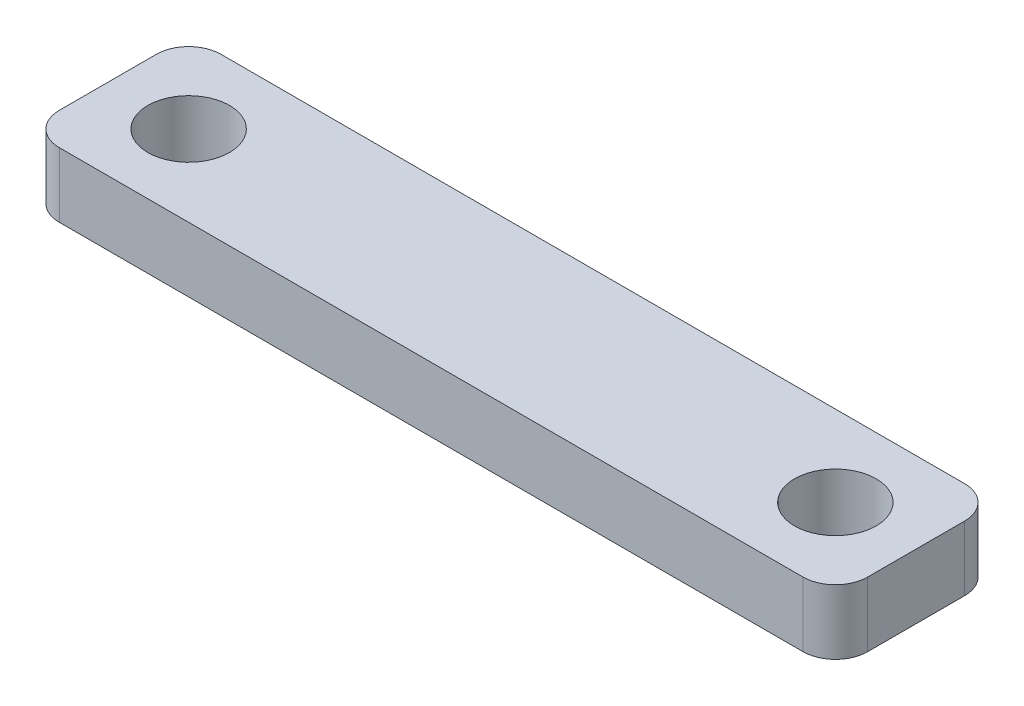
SolidWorks part; units mm, degrees
material "Thornel Mat VMA"
ref_plane "前视基准面" through (0, 0, 0) normal (0, 0, 1) x (1, 0, 0)
ref_plane "上视基准面" through (0, 0, 0) normal (0, 1, 0) x (1, 0, 0)
ref_plane "右视基准面" through (0, 0, 0) normal (1, 0, 0) x (0, 0, -1)
sketch "草图1" plane through (0, 0, 0) normal (0, 1, 0) x (1, 0, 0)
  line L1 (-45, -5) -> (5, -5)
  line L2 (-45, -5) -> (-45, 5)
  line L3 (-45, 5) -> (5, 5)
  line L4 (5, -5) -> (5, 5)
  circle A0 centre (0, 0) radius 2.525
  circle A1 centre (-40, 0) radius 2.525
  point P7 (5, 0)
  dimension "D3" = 5.05
  dimension "D1" = 45
  dimension "D2" = 10
  dimension "D4" = 5
  dimension "D5" = 5
extrude "凸台-拉伸1" add sketch "草图1" along normal blind 4
fillet "圆角1" radius 2 4 edges at (5, 2, -5) (5, 2, 5) (-45, 2, 5) (-45, 2, -5)
